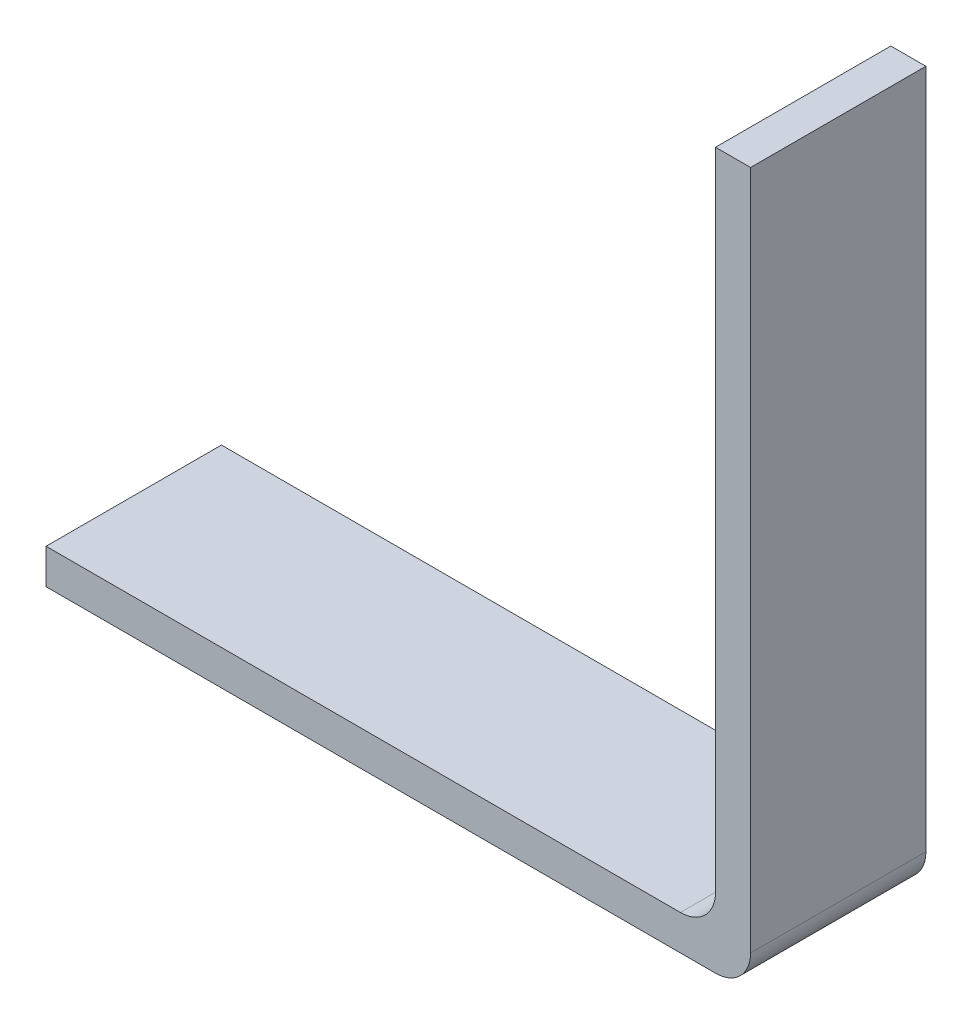
SolidWorks part; units mm, degrees
ref_plane "Ön Düzlem" through (0, 0, 0) normal (0, 0, 1) x (1, 0, 0)
ref_plane "Üst Düzlem" through (0, 0, 0) normal (0, 1, 0) x (1, 0, 0)
ref_plane "Sağ Düzlem" through (0, 0, 0) normal (1, 0, 0) x (0, 0, -1)
sketch "Çizim1" plane through (0, 0, 0) normal (0, 0, 1) x (1, 0, 0)
  line L0 (148.8684, -40.0176) -> (148.8684, -60.4176)
  line L2 (148.8684, -60.4176) -> (128.7778, -60.4176)
extrude "Ekstrüzyon-İnce2" add sketch "Çizim1" along normal blind 5 thin
fillet "Radyus1" radius 1 2 edges at (147.8684, -59.4176, 2.5) (148.8684, -60.4176, 2.5)
